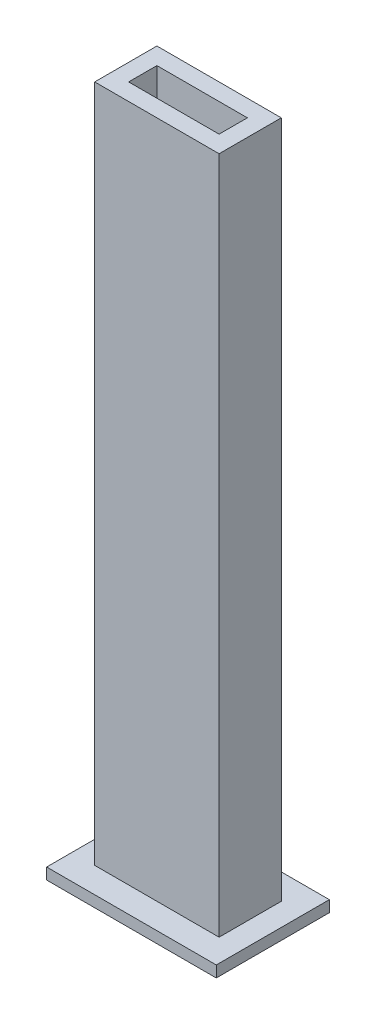
SolidWorks part; units mm, degrees
ref_plane "Front Plane" through (0, 0, 0) normal (0, 0, 1) x (1, 0, 0)
ref_plane "Top Plane" through (0, 0, 0) normal (0, 1, 0) x (1, 0, 0)
ref_plane "Right Plane" through (0, 0, 0) normal (1, 0, 0) x (0, 0, -1)
sketch "Croquis1" plane through (0, 0, 0) normal (0, 1, 0) x (1, 0, 0)
  line L1 (-15, -10) -> (15, -10)
  line L2 (-15, -10) -> (-15, 10)
  line L3 (-15, 10) -> (15, 10)
  line L4 (15, -10) -> (15, 10)
  line L5 (-15, -10) -> (15, 10) construction
  line L6 (-15, 10) -> (15, -10) construction
  point P0 (0, 0)
  dimension "D1" = 30
  dimension "D2" = 20
extrude "Saliente-Extruir1" add sketch "Croquis1" along normal blind 2
sketch "Croquis2" plane through (0, 2, 0) normal (0, 1, 0) x (1, 0, 0)
  line L0 (-11, 5.5) -> (11, 5.5)
  line L1 (-8, -2.5) -> (8, -2.5)
  line L2 (-8, -2.5) -> (-8, 2.5)
  line L3 (-8, 2.5) -> (8, 2.5)
  line L4 (8, -2.5) -> (8, 2.5)
  line L5 (-8, -2.5) -> (8, 2.5) construction
  line L6 (-8, 2.5) -> (8, -2.5) construction
  line L7 (11, -5.5) -> (11, 5.5)
  line L8 (-11, -5.5) -> (11, -5.5)
  line L9 (-11, -5.5) -> (-11, 5.5)
  point P0 (0, 0)
  dimension "D1" = 16
  dimension "D2" = 5
  dimension "D3" = 3
extrude "Saliente-Extruir2" add sketch "Croquis2" along normal blind 120
sketch "Croquis3" plane through (0, 122, 0) normal (0, 1, 0) x (1, 0, 0)
  line L1 (-8, 2.5) -> (8, 2.5)
  line L2 (-8, 2.5) -> (-8, -2.5)
  line L3 (-8, -2.5) -> (8, -2.5)
  line L4 (8, 2.5) -> (8, -2.5)
extrude "Cortar-Extruir1" cut sketch "Croquis3" against normal through all
